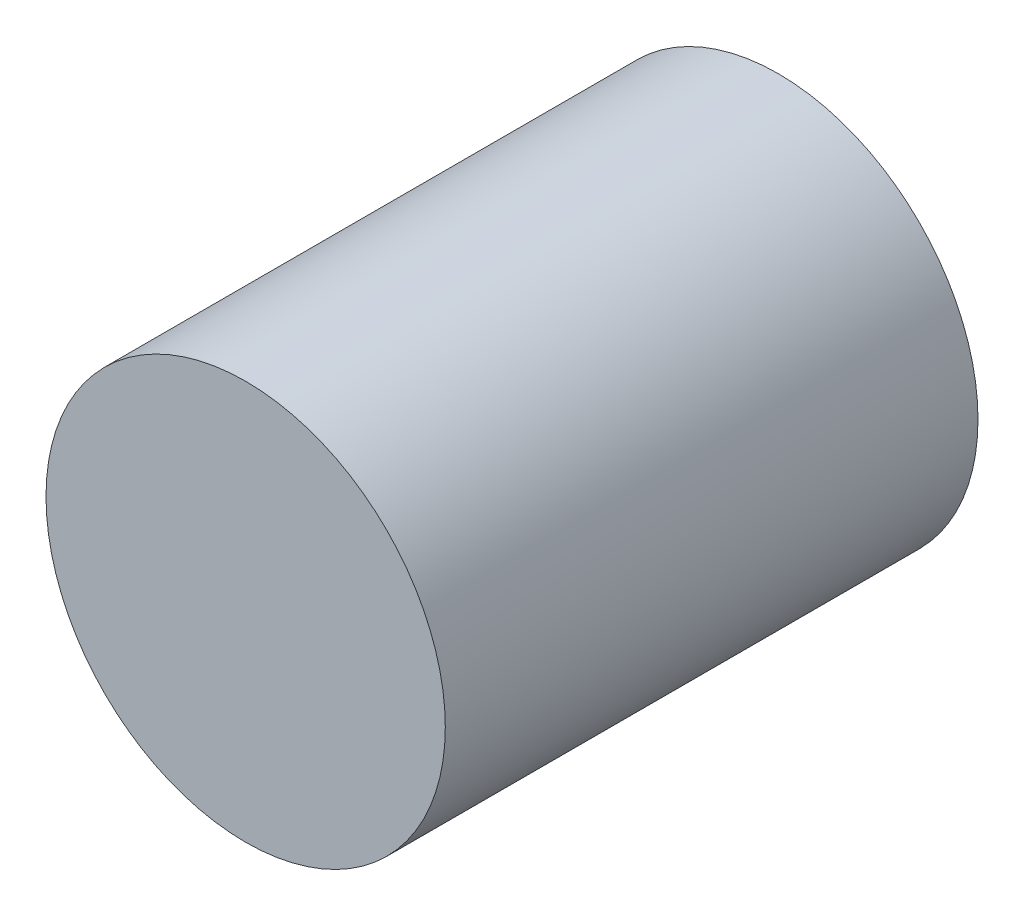
SolidWorks part; units mm, degrees
ref_plane "Front Plane" through (0, 0, 0) normal (0, 0, 1) x (1, 0, 0)
ref_plane "Top Plane" through (0, 0, 0) normal (0, 1, 0) x (1, 0, 0)
ref_plane "Right Plane" through (0, 0, 0) normal (1, 0, 0) x (0, 0, -1)
sketch "Sketch1" plane through (0, 0, 0) normal (0, 0, 1) x (1, 0, 0)
  circle A0 centre (0, 0) radius 4.76
  dimension "D1" = 9.52
extrude "Boss-Extrude1" add sketch "Sketch1" along normal blind 12.7
